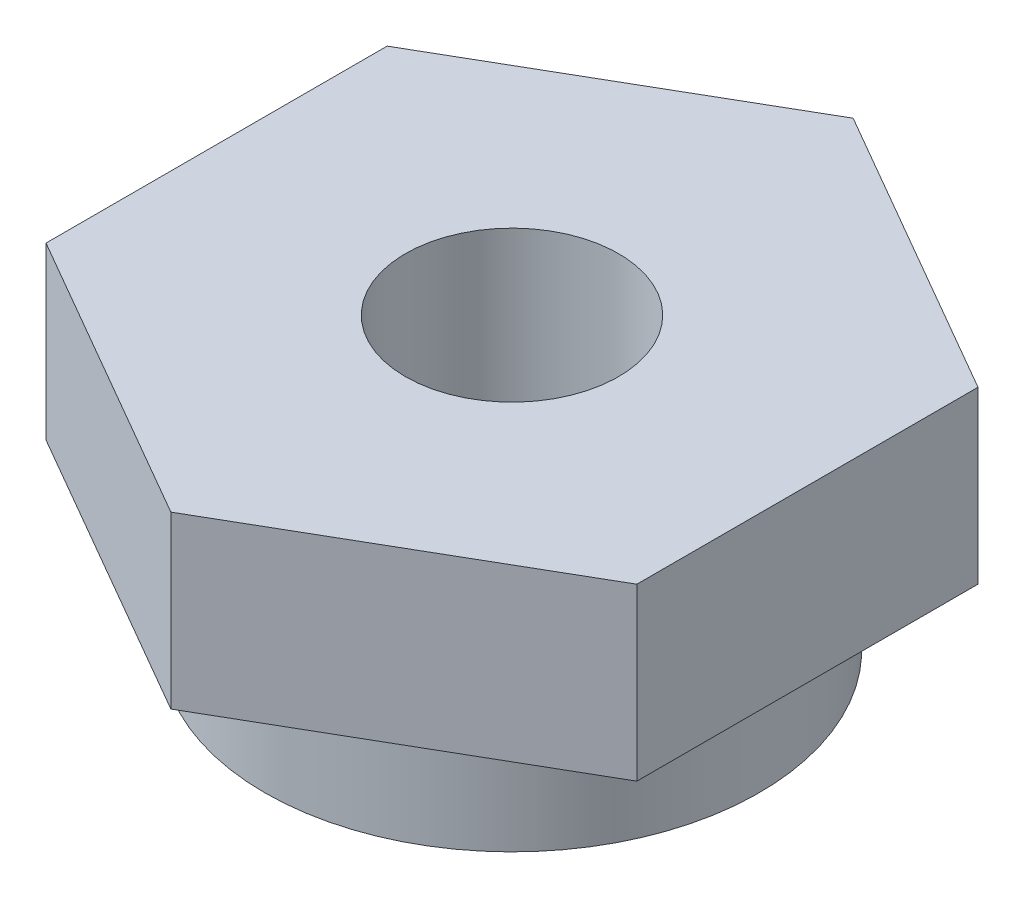
SolidWorks part; units mm, degrees
ref_plane "Front Plane" through (0, 0, 0) normal (0, 0, 1) x (1, 0, 0)
ref_plane "Top Plane" through (0, 0, 0) normal (0, 1, 0) x (1, 0, 0)
ref_plane "Right Plane" through (0, 0, 0) normal (1, 0, 0) x (0, 0, -1)
sketch "Sketch1" plane through (0, 0, 0) normal (0, 1, 0) x (1, 0, 0)
  circle A0 centre (0, 0) radius 3.9688
  circle A1 centre (0, 0) radius 9.2075
  dimension "D1" = 7.9375
  dimension "D2" = 18.415
extrude "Boss-Extrude1" add sketch "Sketch1" along normal blind 4.445
sketch "Sketch2" plane through (0, 4.445, 0) normal (0, 1, 0) x (1, 0, 0)
  line L1 (0, 12.7) -> (-10.9985, 6.35)
  line L2 (-10.9985, 6.35) -> (-10.9985, -6.35)
  line L3 (-10.9985, -6.35) -> (0, -12.7)
  line L4 (0, -12.7) -> (10.9985, -6.35)
  line L5 (10.9985, -6.35) -> (10.9985, 6.35)
  line L6 (10.9985, 6.35) -> (0, 12.7)
  circle A0 centre (0, 0) radius 10.9985 construction
  circle A1 centre (0, 0) radius 3.9688
  circle A2 centre (0, 0) radius 3.9688 construction
  dimension "D1" = 25.4
extrude "Boss-Extrude2" add sketch "Sketch2" along normal blind 6.35
